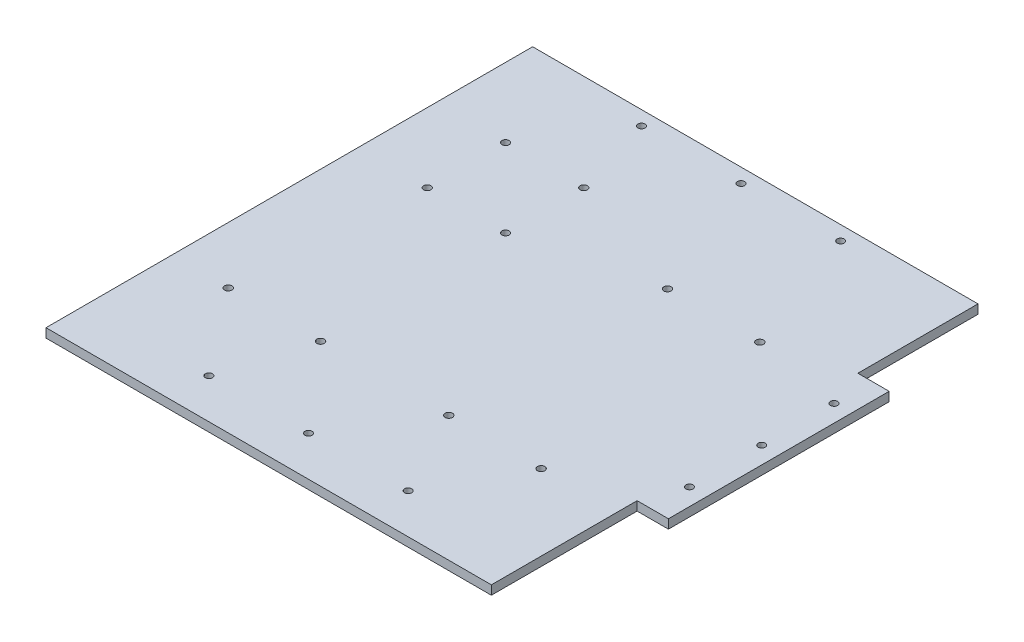
SolidWorks part; units mm, degrees
material "Cedar"
ref_plane "Front Plane" through (0, 0, 0) normal (0, 0, 1) x (1, 0, 0)
ref_plane "Top Plane" through (0, 0, 0) normal (0, 1, 0) x (1, 0, 0)
ref_plane "Right Plane" through (0, 0, 0) normal (1, 0, 0) x (0, 0, -1)
sketch "Sketch1" plane through (0, 0, 0) normal (0, 1, 0) x (1, 0, 0)
  line L0 (72.8376, -16.2766) -> (72.8376, -52.4668) construction
  line L1 (-156.5, -171) -> (156.5, -171)
  line L2 (-156.5, -171) -> (-156.5, 171)
  line L3 (-156.5, 171) -> (156.5, 171)
  line L4 (156.5, -171) -> (156.5, 171)
  line L5 (-156.5, -171) -> (156.5, 171) construction
  line L6 (-156.5, 171) -> (156.5, -171) construction
  point P0 (0, 0)
  dimension "D1" = 342
  dimension "D2" = 313
extrude "Boss-Extrude1" add sketch "Sketch1" against normal blind 6.35
ref_plane "Plane1" through (0, 0, -9) normal (0, 0, -1) x (-1, 0, 0)
sketch "Sketch3" plane through (0, 0, 0) normal (0, 1, 0) x (1, 0, 0)
  line L0 (156.5, 9) -> (-156.5, 9) construction
  line L1 (156.5, -171) -> (156.5, 171) construction
  line L2 (-156.5, 171) -> (-156.5, -171) construction
  line L3 (55, 9) -> (-55, 9) construction
  line L4 (156.5, 86.5702) -> (156.5, -68.5702)
  line L5 (156.5, -68.5702) -> (178.5, -68.5702)
  line L6 (178.5, -68.5702) -> (178.5, 86.5702)
  line L7 (178.5, 86.5702) -> (156.5, 86.5702)
  circle A0 centre (166.5, 9) radius 2.5
  circle A1 centre (166.5, -41.8) radius 2.5
  circle A2 centre (166.5, 59.8) radius 2.5
  point P10 (156.5, 9)
  dimension "D2" = 5
  dimension "D4" = 5
  dimension "D5" = 50.8
  dimension "D1" = 22
  dimension "D3" = 10
extrude "Boss-Extrude2" add sketch "Sketch3" against normal blind 6.35
sketch "Sketch2" plane through (0, 0, 0) normal (0, 1, 0) x (1, 0, 0)
  line L0 (156.5, 9) -> (-156.5, 9) construction
  line L1 (156.5, -171) -> (156.5, -68.5702) construction
  line L2 (-156.5, 171) -> (-156.5, -171) construction
  line L3 (0, -143) -> (0, -171) construction
  line L4 (55, 9) -> (-55, 9) construction
  line L5 (156.5, -143) -> (-156.5, -143) construction
  line L6 (-156.5, -171) -> (156.5, -171) construction
  circle A0 centre (0, -143) radius 2.5
  circle A1 centre (-70, -143) radius 2.5
  circle A2 centre (70, -143) radius 2.5
  circle A3 centre (-70, 161) radius 2.5
  circle A4 centre (0, 161) radius 2.5
  circle A5 centre (70, 161) radius 2.5
  dimension "D2" = 5
  dimension "D3" = 5
  dimension "D4" = 70
  dimension "D1" = 152
extrude "Cut-Extrude1" cut sketch "Sketch2" against normal through all
sketch "Sketch4" plane through (0, 0, 0) normal (0, 1, 0) x (1, 0, 0)
  circle A20 centre (103.2497, -82.7833) radius 2.6
  circle A21 centre (38.3497, -82.7833) radius 2.6
  circle A22 centre (-51.7503, -82.7833) radius 2.6
  circle A23 centre (-116.6503, -82.7833) radius 2.6
  circle A24 centre (103.1563, 71.0103) radius 2.6
  circle A25 centre (38.2563, 71.0103) radius 2.6
  circle A26 centre (-52.6875, 48.131) radius 2.55
  circle A27 centre (-107.6875, 48.131) radius 2.55
  circle A28 centre (-52.6875, 103.131) radius 2.55
  circle A29 centre (-107.6875, 103.131) radius 2.55
extrude "Cut-Extrude2" cut sketch "Sketch4" against normal through all
